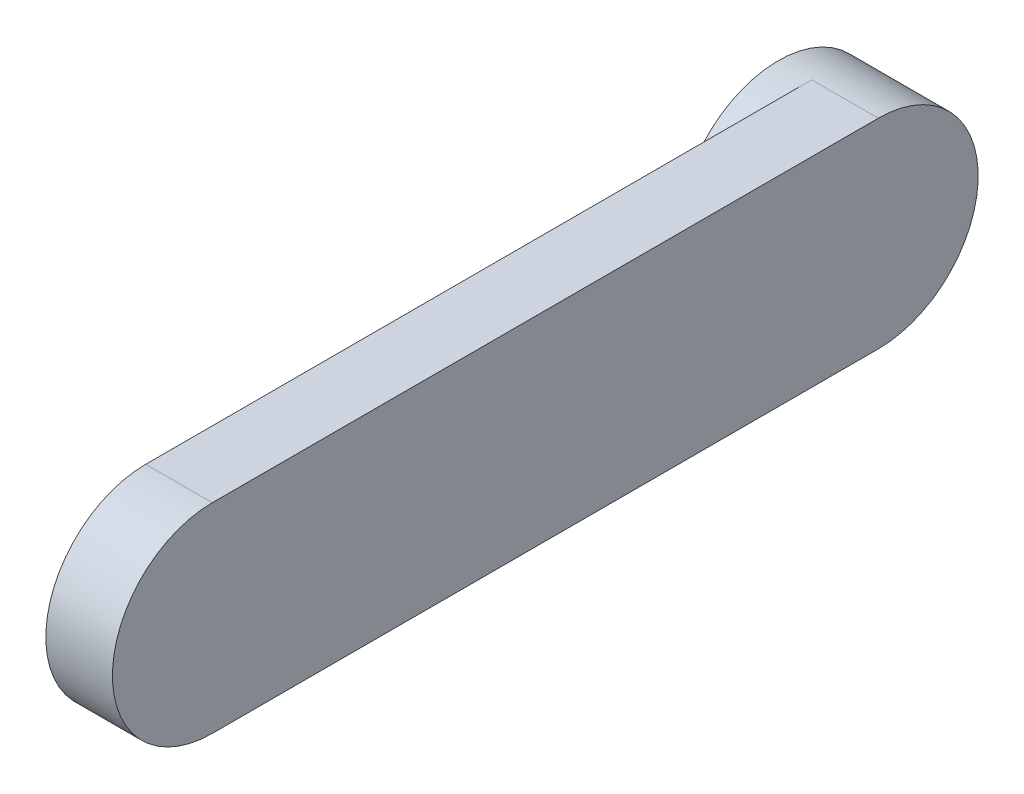
SolidWorks part; units mm, degrees
ref_plane "前视基准面" through (0, 0, 0) normal (0, 0, 1) x (1, 0, 0)
ref_plane "上视基准面" through (0, 0, 0) normal (0, 1, 0) x (1, 0, 0)
ref_plane "右视基准面" through (0, 0, 0) normal (1, 0, 0) x (0, 0, -1)
sketch "草图1" plane through (0, 0, 0) normal (1, 0, 0) x (0, 0, -1)
  line L0 (0, 30) -> (-200, 30)
  line L1 (0, -30) -> (-200, -30)
  arc A1 (0, 30) -> (0, -30) centre (0, 0) cw
  arc A2 (-200, 30) -> (-200, -30) centre (-200, 0) ccw
extrude "凸台-拉伸1" add sketch "草图1" along normal blind 20
sketch "草图2" plane through (0, 0, 0) normal (-1, 0, 0) x (0, 0, 1)
  circle A0 centre (0, 0) radius 30
extrude "凸台-拉伸2" add sketch "草图2" along normal blind 10
